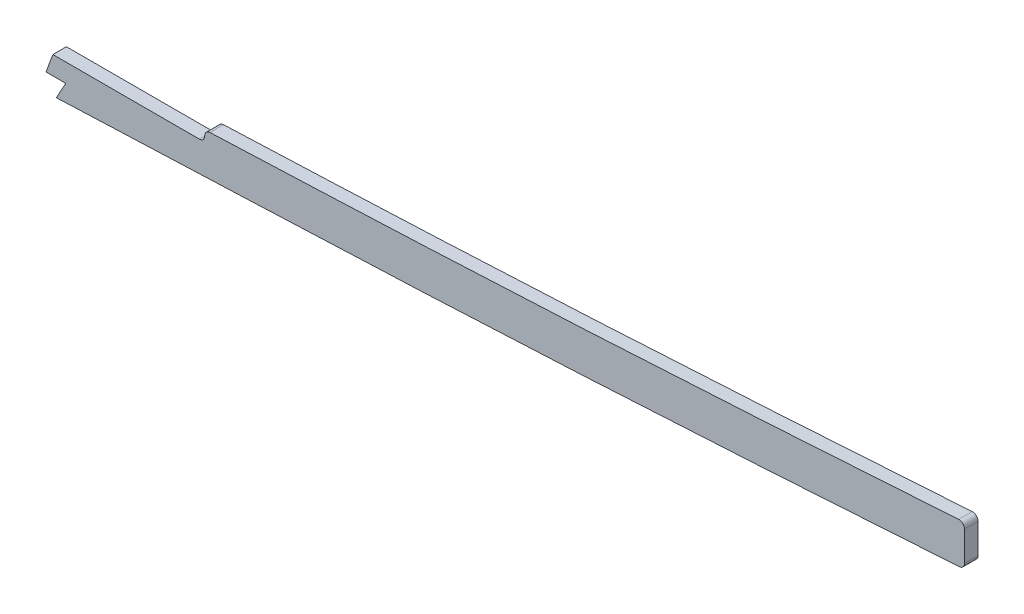
SolidWorks part; units mm, degrees
ref_plane "Front Plane" through (0, 0, 0) normal (0, 0, 1) x (1, 0, 0)
ref_plane "Top Plane" through (0, 0, 0) normal (0, 1, 0) x (1, 0, 0)
ref_plane "Right Plane" through (0, 0, 0) normal (1, 0, 0) x (0, 0, -1)
sketch "Sketch1" plane through (0, 0, 0) normal (0, 0, 1) x (1, 0, 0)
  line L0 (1046.2855, 53.4707) -> (499.61, 53.4707) construction
  line L1 (55, 0) -> (-55, 0) construction
  line L2 (1046.2855, -53.4707) -> (499.61, -53.4707)
  line L3 (1046.2855, -34.4207) -> (499.61, -34.4207)
  line L4 (99.06, -18.1493) -> (99.06, -37.7415)
  line L5 (2669.54, 9.5231) -> (2669.54, -9.569)
  spline S0 degree 5 poles (2699.7923, 7.5245) (2639.6368, 11.6572) (2579.4813, 15.4358) (2518.4981, 19.1485) (2436.3555, 23.2524) (2354.213, 26.6315) (2332.5703, 27.481) (2156.2686, 34.3778) (1979.9669, 41.6286) (1824.1143, 52.7713) (1636.9286, 53.5796) (1449.7429, 53.454) (1418.0067, 53.4707) (1324.8993, 53.4707) (1231.7919, 53.4707) (1170.4413, 53.4707) (1108.7841, 53.4707) (1047.1269, 53.4707) (1046.8464, 53.4707) (1046.5659, 53.4707) (1046.2855, 53.4707) knots 100.654805 100.654805 100.654805 100.654805 100.654805 100.654805 130.927897 130.927897 130.927897 141.337055 141.337055 141.337055 218.101815 218.101815 218.101815 233.772059 233.772059 233.772059 264.077723 264.077723 264.077723 264.216209 264.216209 264.216209 264.216209 264.216209 264.216209 weights 1 1 1 1 1 1 1 1 1 1 1 1 1 1 1 1 1 1 1 1 1 construction
  spline S1 degree 5 poles (499.61, 53.4707) (492.1368, 53.4707) (484.7543, 53.4707) (477.443, 53.4707) (448.5166, 53.4707) (419.5901, 53.4707) (398.3681, 53.4707) (355.6475, 53.4707) (312.927, 53.4707) (289.2351, 53.4703) (265.365, 53.4707) (241.4948, 53.4707) (241.4716, 53.4707) (241.4484, 53.4707) (241.4251, 53.4707) knots 19.90683 19.90683 19.90683 19.90683 19.90683 19.90683 23.637897 23.637897 23.637897 34.276546 34.276546 34.276546 46.401341 46.401341 46.401341 46.413154 46.413154 46.413154 46.413154 46.413154 46.413154 weights 1 1 1 1 1 1 1 1 1 1 1 1 1 1 1 construction
  spline S2 degree 5 poles (241.4251, 53.4707) (224.2869, 53.4707) (207.1495, 53.4673) (190.2039, 52.6866) (151.6561, 49.0319) (113.1083, 41.5037) (91.9499, 36.3426) (71.313, 30.9696) (50.6762, 24.7565) knots 0 0 0 0 0 0 8.713816 8.713816 8.713816 19.90683 19.90683 19.90683 19.90683 19.90683 19.90683 weights 1 1 1 1 1 1 1 1 1 construction
  spline S3 degree 5 poles (241.4251, -53.4707) (224.2869, -53.4707) (207.1495, -53.4673) (190.2039, -52.6866) (151.6561, -49.0319) (113.1083, -41.5037) (91.9499, -36.3426) (71.313, -30.9696) (50.6762, -24.7565) knots 0 0 0 0 0 0 8.713816 8.713816 8.713816 19.90683 19.90683 19.90683 19.90683 19.90683 19.90683 weights 1 1 1 1 1 1 1 1 1
  spline S4 degree 5 poles (499.61, -53.4707) (492.1368, -53.4707) (484.7543, -53.4707) (477.443, -53.4707) (448.5166, -53.4707) (419.5901, -53.4707) (398.3681, -53.4707) (355.6475, -53.4707) (312.927, -53.4707) (289.2351, -53.4703) (265.365, -53.4707) (241.4948, -53.4707) (241.4716, -53.4707) (241.4484, -53.4707) (241.4251, -53.4707) knots 19.90683 19.90683 19.90683 19.90683 19.90683 19.90683 23.637897 23.637897 23.637897 34.276546 34.276546 34.276546 46.401341 46.401341 46.401341 46.413154 46.413154 46.413154 46.413154 46.413154 46.413154 weights 1 1 1 1 1 1 1 1 1 1 1 1 1 1 1
  spline S5 degree 5 poles (2699.7923, -7.5245) (2639.6368, -11.6572) (2579.4813, -15.4358) (2518.4981, -19.1485) (2436.3555, -23.2524) (2354.213, -26.6315) (2332.5703, -27.481) (2156.2686, -34.3778) (1979.9669, -41.6286) (1824.1143, -52.7713) (1636.9286, -53.5796) (1449.7429, -53.454) (1418.0067, -53.4707) (1324.8993, -53.4707) (1231.7919, -53.4707) (1170.4413, -53.4707) (1108.7841, -53.4707) (1047.1269, -53.4707) (1046.8464, -53.4707) (1046.5659, -53.4707) (1046.2855, -53.4707) knots 100.654805 100.654805 100.654805 100.654805 100.654805 100.654805 130.927897 130.927897 130.927897 141.337055 141.337055 141.337055 218.101815 218.101815 218.101815 233.772059 233.772059 233.772059 264.077723 264.077723 264.077723 264.216209 264.216209 264.216209 264.216209 264.216209 264.216209 weights 1 1 1 1 1 1 1 1 1 1 1 1 1 1 1 1 1 1 1 1 1
  spline S6 degree 1 poles (2698.4867, 11.4807) (1046.2855, -34.4207) knots 0 0 1 1 construction
  spline S7 degree 1 poles (499.61, -34.4207) (241.4252, -34.4207) knots 0 0 1 1 construction
  spline S8 degree 1 poles (241.4252, -34.4207) (56.168, -6.5153) knots 0 0 1 1 construction
  spline S9 degree 3 poles (2698.4867, 11.4807) (2691.2474, 10.9833) (2679.1952, 10.1655) (2662.2765, 9.0388) (2635.6663, 7.2925) (2596.8577, 4.8261) (2545.7297, 1.7583) (2494.4053, -1.0986) (2451.533, -3.2666) (2417.1983, -4.8671) (2391.4571, -6.0036) (2365.6347, -7.0869) (2339.5463, -8.1377) (2313.4661, -9.1651) (2287.6124, -10.1795) (2261.7633, -11.201) (2227.2853, -12.5838) (2184.1756, -14.3661) (2132.4291, -16.6074) (2063.4255, -19.7089) (1977.1749, -23.7005) (1873.7325, -28.1494) (1770.3746, -31.6575) (1667.0857, -33.7931) (1581.0111, -34.3832) (1512.074, -34.4278) (1443.0615, -34.4095) (1356.8009, -34.4244) (1218.7946, -34.4185) (1115.289, -34.4207) (1046.2855, -34.4207) knots 100.654805 100.654805 100.654805 100.654805 102.842388 104.300777 105.766098 110.877392 115.988686 121.09998 126.211274 128.766921 131.322568 133.878215 136.433862 138.989509 141.545156 144.100803 146.656449 151.767743 156.879037 161.990331 172.212919 182.435507 192.658094 202.880682 213.10327 218.214564 223.325858 233.548445 243.771033 264.216209 264.216209 264.216209 264.216209
  spline S10 degree 3 poles (499.61, -34.4207) (488.6147, -34.4207) (472.2364, -34.4207) (449.9402, -34.4207) (427.7713, -34.4207) (405.8747, -34.4207) (384.5849, -34.4207) (368.9002, -34.4207) (353.3766, -34.4207) (332.6085, -34.4207) (306.2878, -34.4206) (274.0235, -34.4205) (252.271, -34.4207) (241.4252, -34.4207) knots 19.90683 19.90683 19.90683 19.90683 23.22012 24.876765 26.533411 29.846701 31.503346 33.159992 34.816637 36.473282 39.786573 43.099863 46.413154 46.413154 46.413154 46.413154
  spline S11 degree 3 poles (241.4252, -34.4207) (239.3949, -34.4207) (235.3223, -34.4205) (227.2744, -34.3987) (217.3194, -34.2975) (205.5307, -33.9764) (189.9633, -33.2126) (170.697, -31.5435) (147.5333, -28.3144) (125.4828, -24.2021) (107.4399, -20.1965) (92.2061, -16.4882) (75.9505, -12.2555) (63.6202, -8.7589) (56.168, -6.5153) knots 0 0 0 0 0.622088 1.244177 2.488354 3.732531 4.976707 7.465061 9.953415 12.441768 14.558235 15.802412 17.418476 19.90683 19.90683 19.90683 19.90683
  point P2 (0, 0)
  dimension "D1" = 50.6762
  dimension "D3" = 99.06
  dimension "D4" = 2669.54
  dimension "D2" = 19.05
extrude "Boss-Extrude1" add sketch "Sketch1" along normal mid plane 6.35 contours S10 S11 L4 S3 S4 L2 S5 L5 S9 L3
sketch "Sketch2" plane through (0, 0, 3.175) normal (0, 0, 1) x (1, 0, 0)
  line L0 (2187.01, -14.2633) -> (2312.9875, -14.2633)
  line L1 (2312.9875, -14.2633) -> (2312.9875, -9.1833)
  spline S0 degree 3 poles (689.0175, 232.3189) (4033.8285, 148.9311) (3356.6623, 54.6077) (2635.6663, 7.2925) (2596.8577, 4.8261) (2545.7297, 1.7583) (2494.4053, -1.0986) (2451.533, -3.2666) (2417.1983, -4.8671) (2391.4571, -6.0036) (2365.6347, -7.0869) (2339.5463, -8.1377) (2313.4661, -9.1651) (2287.6124, -10.1795) (2261.7633, -11.201) (2227.2853, -12.5838) (2184.1756, -14.3661) (2132.4291, -16.6074) (2063.4255, -19.7089) (1977.1749, -23.7005) (1873.7325, -28.1494) (1770.3746, -31.6575) (1667.0857, -33.7931) (1581.0111, -34.3832) (1512.074, -34.4278) (1443.0615, -34.4095) (1356.8009, -34.4244) (551.9641, -34.3896) (-218.4198, -34.7282) (-953.6342, -29.9632) knots -106.828462 -106.828462 -106.828462 -106.828462 104.300777 105.766098 110.877392 115.988686 121.09998 126.211274 128.766921 131.322568 133.878215 136.433862 138.989509 141.545156 144.100803 146.656449 151.767743 156.879037 161.990331 172.212919 182.435507 192.658094 202.880682 213.10327 218.214564 223.325858 233.548445 243.771033 461.793666 461.793666 461.793666 461.793666 only from (2669.54, 9.5231) to (1046.2855, -34.4207) construction
  spline S1 degree 3 poles (2669.54, 9.5231) (2667.1265, 9.3624) (2659.8616, 8.8803) (2635.6663, 7.2925) (2596.8577, 4.8261) (2545.7297, 1.7583) (2494.4053, -1.0986) (2451.533, -3.2666) (2417.1983, -4.8671) (2391.4571, -6.0036) (2365.6347, -7.0869) (2339.5463, -8.1377) (2313.4661, -9.1651) (2287.6124, -10.1795) (2261.7633, -11.201) (2227.2853, -12.5838) (2184.1756, -14.3661) (2132.4291, -16.6074) (2063.4255, -19.7089) (1977.1749, -23.7005) (1873.7325, -28.1494) (1770.3746, -31.6575) (1667.0857, -33.7931) (1581.0111, -34.3832) (1512.074, -34.4278) (1443.0615, -34.4095) (1356.8009, -34.4244) (1218.7946, -34.4185) (1115.289, -34.4207) (1046.2855, -34.4207) knots 103.571583 103.571583 103.571583 103.571583 104.300777 105.766098 110.877392 115.988686 121.09998 126.211274 128.766921 131.322568 133.878215 136.433862 138.989509 141.545156 144.100803 146.656449 151.767743 156.879037 161.990331 172.212919 182.435507 192.658094 202.880682 213.10327 218.214564 223.325858 233.548445 243.771033 264.216209 264.216209 264.216209 264.216209
  point P2 (0, 0)
  spline M9 degree 3 poles (2698.4867, 11.4807) (2691.2474, 10.9833) (2679.1952, 10.1655) (2662.2765, 9.0388) (2635.6663, 7.2925) (2596.8577, 4.8261) (2545.7297, 1.7583) (2494.4053, -1.0986) (2451.533, -3.2666) (2417.1983, -4.8671) (2391.4571, -6.0036) (2365.6347, -7.0869) (2339.5463, -8.1377) (2313.4661, -9.1651) (2287.6124, -10.1795) (2261.7633, -11.201) (2227.2853, -12.5838) (2184.1756, -14.3661) (2132.4291, -16.6074) (2063.4255, -19.7089) (1977.1749, -23.7005) (1873.7325, -28.1494) (1770.3746, -31.6575) (1667.0857, -33.7931) (1581.0111, -34.3832) (1512.074, -34.4278) (1443.0615, -34.4095) (1356.8009, -34.4244) (1218.7946, -34.4185) (1115.289, -34.4207) (1046.2855, -34.4207) knots 100.654805 100.654805 100.654805 100.654805 102.842388 104.300777 105.766098 110.877392 115.988686 121.09998 126.211274 128.766921 131.322568 133.878215 136.433862 138.989509 141.545156 144.100803 146.656449 151.767743 156.879037 161.990331 172.212919 182.435507 192.658094 202.880682 213.10327 218.214564 223.325858 233.548445 243.771033 264.216209 264.216209 264.216209 264.216209 only from (2669.54, 9.5231) to (1046.2855, -34.4207)
  dimension "D1" = 2312.9875
  dimension "D2" = 5.08
extrude "Cut-Extrude1" cut sketch "Sketch2" against normal through all contours L0 L1 M9
fillet "Fillet1" radius 2.54 6 edges at (2669.54, -9.569, 0) (2669.54, 9.5231, 0) (99.06, -37.7415, 0) (99.06, -18.1493, 0) (2312.9875, -14.2633, 0)
sketch "Sketch3" plane through (0, 0, 3.175) normal (0, 0, 1) x (1, 0, 0)
  line L9 (2187.01, -14.2633) -> (2310.4475, -14.2633) construction
  line L25 (2241.7242, -14.2633) -> (2238.4954, -22.96)
  line L26 (2238.4954, -22.96) -> (2247.7774, -22.96)
  line L27 (2247.7774, -22.96) -> (2243.3377, -31.0069)
  line L28 (2241.7242, -14.2633) -> (2241.7242, 0)
  line L29 (2241.7242, 0) -> (-136.4301, 149.2308)
  line L30 (-44.7672, -591.1235) -> (2243.3377, -46.2049)
  line L31 (-44.7672, -591.1235) -> (-136.4301, 149.2308)
  line L32 (2243.3377, -46.2049) -> (2243.3377, -31.0069)
  spline S3 degree 5 poles (2667.1682, -9.7266) (2613.4902, -13.2886) (2559.6385, -16.6207) (2505.242, -19.8061) (2429.7275, -23.525) (2354.213, -26.6315) (2332.5703, -27.481) (2156.2686, -34.3778) (1979.9669, -41.6286) (1824.1143, -52.7713) (1636.9286, -53.5796) (1449.7429, -53.454) (1418.0067, -53.4707) (1324.8993, -53.4707) (1231.7919, -53.4707) (1170.4413, -53.4707) (1108.7841, -53.4707) (1047.1269, -53.4707) (1046.8464, -53.4707) (1046.5659, -53.4707) (1046.2855, -53.4707) knots 103.937447 103.937447 103.937447 103.937447 103.937447 103.937447 130.927897 130.927897 130.927897 141.337055 141.337055 141.337055 218.101815 218.101815 218.101815 233.772059 233.772059 233.772059 264.077723 264.077723 264.077723 264.216209 264.216209 264.216209 264.216209 264.216209 264.216209 weights 1 1 1 1 1 1 1 1 1 1 1 1 1 1 1 1 1 1 1 1 1 construction
extrude "Cut-Extrude2" cut sketch "Sketch3" against normal blind 7.62
